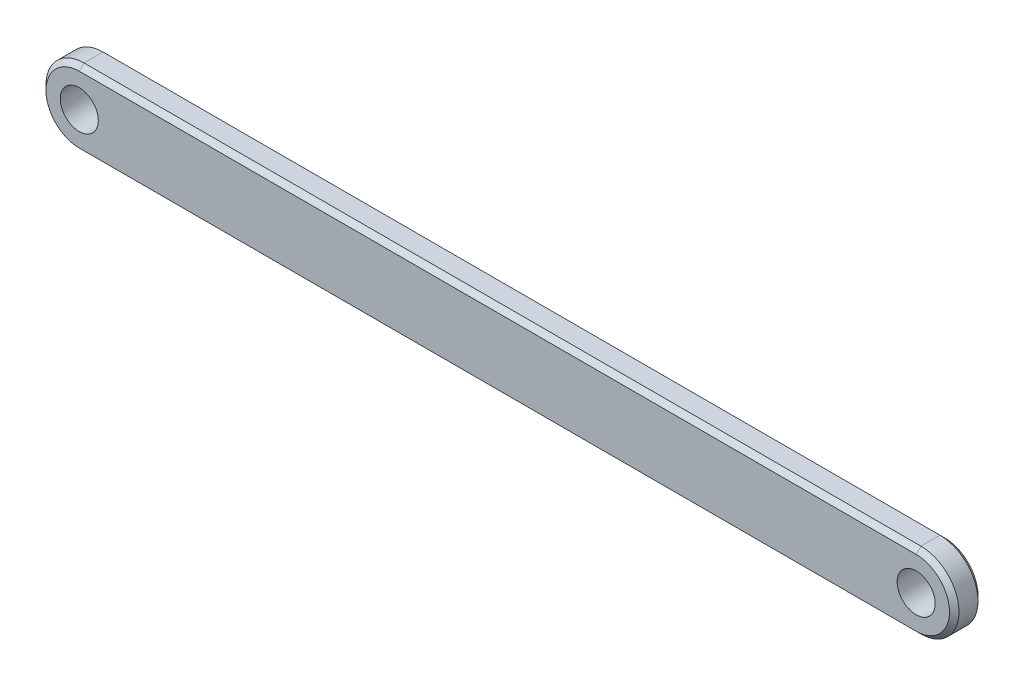
SolidWorks part; units mm, degrees
ref_plane "Front Plane" through (0, 0, 0) normal (0, 0, 1) x (1, 0, 0)
ref_plane "Top Plane" through (0, 0, 0) normal (0, 1, 0) x (1, 0, 0)
ref_plane "Right Plane" through (0, 0, 0) normal (1, 0, 0) x (0, 0, -1)
sketch "Sketch1" plane through (0, 0, 0) normal (0, 0, 1) x (1, 0, 0)
  line L0 (-44, 0) -> (44, 0) construction
  line L1 (-44, 4) -> (44, 4)
  line L2 (-44, -4) -> (44, -4)
  arc A0 (-44, 4) -> (-44, -4) centre (-44, 0) ccw
  arc A1 (44, -4) -> (44, 4) centre (44, 0) ccw
  circle A2 centre (-44, 0) radius 2
  circle A3 centre (44, 0) radius 2
  point P2 (0, 0)
  dimension "D1" = 4
  dimension "D3" = 4
  dimension "D2" = 88
extrude "Boss-Extrude1" add sketch "Sketch1" along normal mid plane 3
chamfer "Chamfer1" distance 0.5 angle 45 8 edges at (48, 0, -1.5) (0, 4, -1.5) (0, -4, -1.5) (-48, 0, -1.5) (48, 0, 1.5) (0, 4, 1.5) (0, -4, 1.5) (-48, 0, 1.5)
